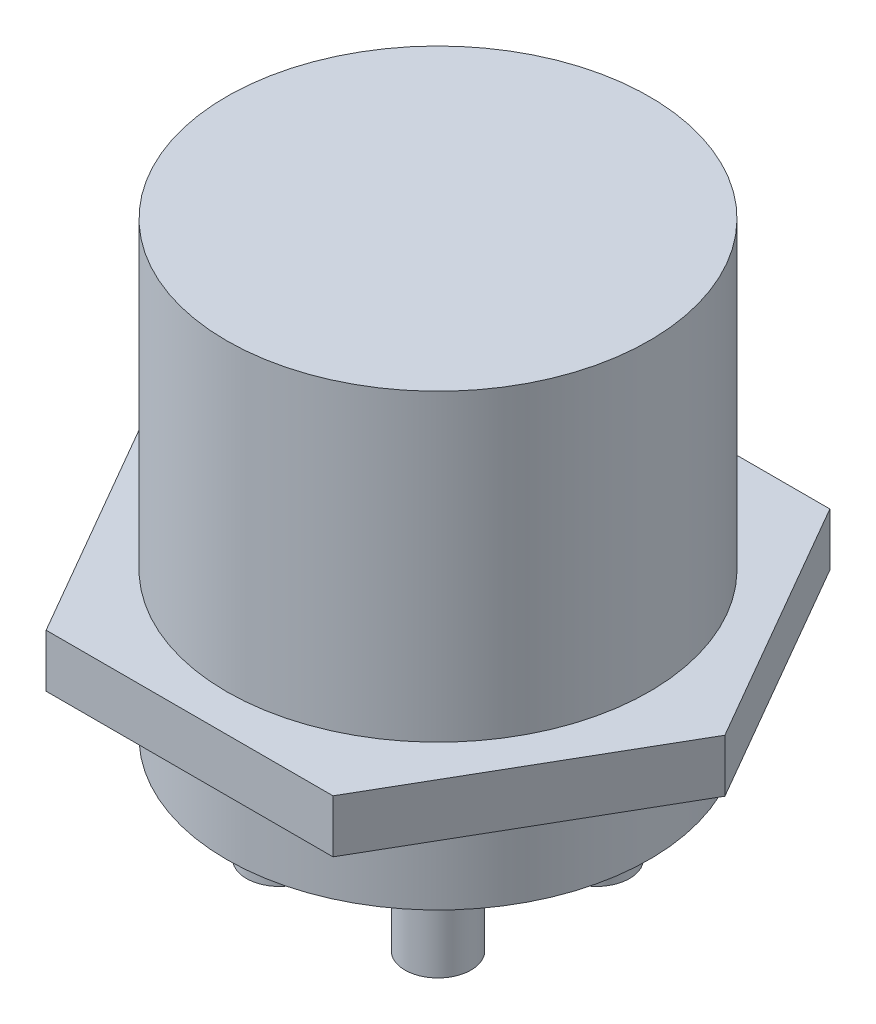
SolidWorks part; units mm, degrees
ref_plane "Front Plane" through (0, 0, 0) normal (0, 0, 1) x (1, 0, 0)
ref_plane "Top Plane" through (0, 0, 0) normal (0, 1, 0) x (1, 0, 0)
ref_plane "Right Plane" through (0, 0, 0) normal (1, 0, 0) x (0, 0, -1)
sketch "Sketch1" plane through (0, 0, 0) normal (0, 1, 0) x (1, 0, 0)
  circle A0 centre (0, 0) radius 8
  dimension "D1" = 16
extrude "Boss-Extrude1" add sketch "Sketch1" along normal mid plane 17
sketch "Sketch2" plane through (0, -8.5, 0) normal (0, -1, 0) x (1, 0, 0)
  line L0 (0, 8) -> (0, -8) construction
  line L1 (-8, 0) -> (8, 0) construction
  circle A0 centre (0, 0) radius 8 construction
  circle A1 centre (-3, 3) radius 1.25
  circle A2 centre (3, 3) radius 1.25
  circle A3 centre (3, -3) radius 1.25
  circle A4 centre (-3, -3) radius 1.25
  dimension "D1" = 2.5
  dimension "D2" = 3
  dimension "D3" = 3
extrude "Boss-Extrude2" add sketch "Sketch2" along normal blind 4 separate body
sketch "Sketch3" plane through (0, 0, 0) normal (0, 1, 0) x (1, 0, 0)
  line L1 (10.8542, 0) -> (5.4271, 9.4)
  line L2 (5.4271, 9.4) -> (-5.4271, 9.4)
  line L3 (-5.4271, 9.4) -> (-10.8542, 0)
  line L4 (-10.8542, 0) -> (-5.4271, -9.4)
  line L5 (-5.4271, -9.4) -> (5.4271, -9.4)
  line L6 (5.4271, -9.4) -> (10.8542, 0)
  circle A0 centre (0, 0) radius 9.4 construction
  dimension "D1" = 18.8
  dimension "D2" = 9.4
extrude "Boss-Extrude3" add sketch "Sketch3" against normal blind 2 from offset 3 separate body offset against normal yes
